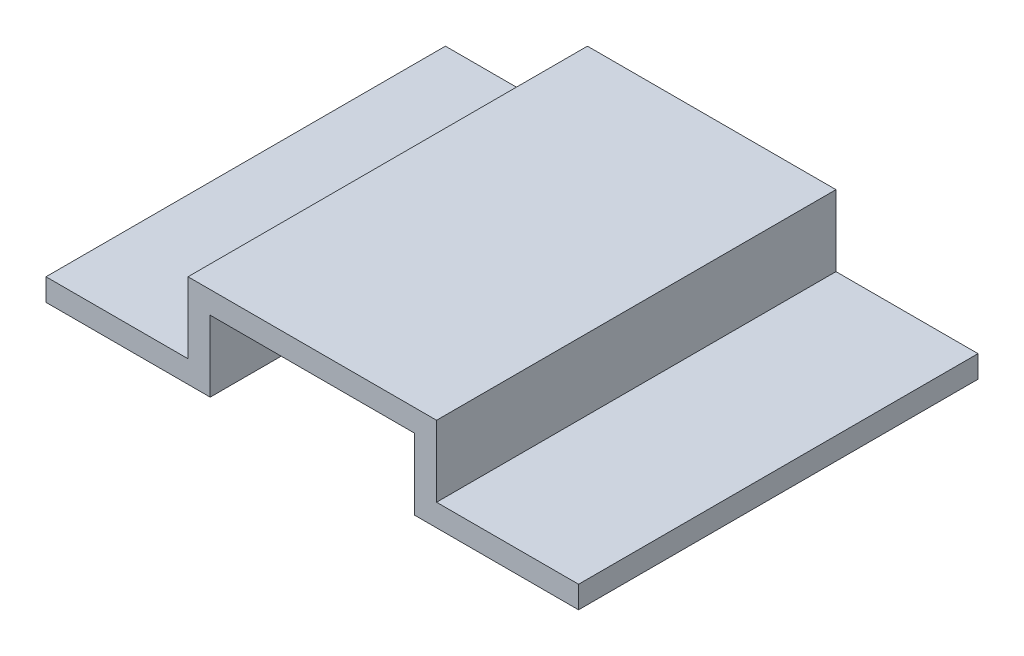
SolidWorks part; units mm, degrees
ref_plane "Front Plane" through (0, 0, 0) normal (0, 0, 1) x (1, 0, 0)
ref_plane "Top Plane" through (0, 0, 0) normal (0, 1, 0) x (1, 0, 0)
ref_plane "Right Plane" through (0, 0, 0) normal (1, 0, 0) x (0, 0, -1)
sketch "Sketch1" plane through (0, 0, 0) normal (0, 0, 1) x (1, 0, 0)
  line L0 (50, 0) -> (235, 0)
  line L1 (235, 0) -> (235, 80)
  line L2 (235, 80) -> (465, 80)
  line L6 (50, 25) -> (210, 25)
  line L7 (210, 25) -> (210, 105)
  line L8 (210, 105) -> (490, 105)
  line L12 (350, 105) -> (350, 80) construction
  line L18 (50, 25) -> (50, 0)
  line L19 (650, 25) -> (650, 0)
  line L20 (490, 25) -> (490, 105)
  line L21 (650, 25) -> (490, 25)
  line L22 (465, 0) -> (465, 80)
  line L23 (650, 0) -> (465, 0)
  dimension "D1" = 25
  dimension "D2" = 350
  dimension "D3" = 25
  dimension "D4" = 25
  dimension "D5" = 115
  dimension "D6" = 80
  dimension "D7" = 50
extrude "Boss-Extrude1" add sketch "Sketch1" along normal blind 450 contours L8 L20 L21 L19 L23 L22 L2 L1 L0 L18 L6 L7
